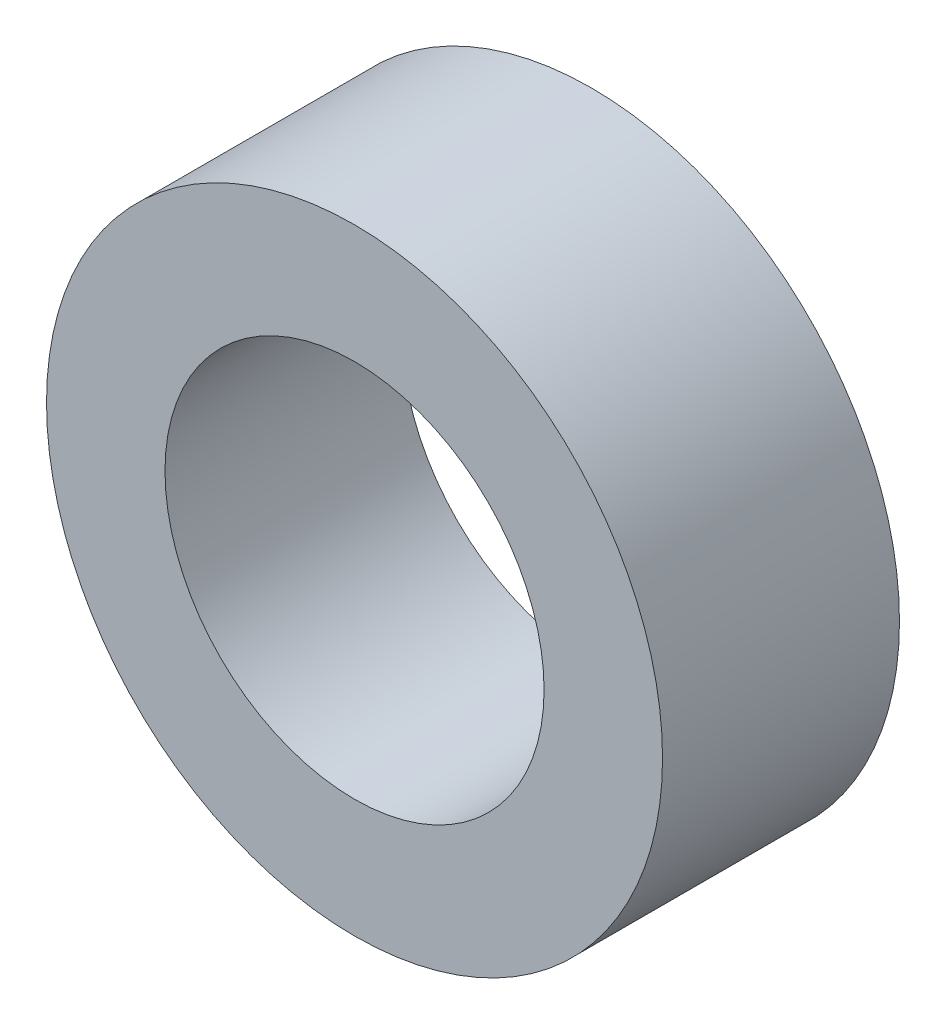
SolidWorks part; units mm, degrees
material "ABS"
ref_plane "Спереди" through (0, 0, 0) normal (0, 0, 1) x (1, 0, 0)
ref_plane "Сверху" through (0, 0, 0) normal (0, 1, 0) x (1, 0, 0)
ref_plane "Справа" through (0, 0, 0) normal (1, 0, 0) x (0, 0, -1)
sketch "Эскиз1" plane through (0, 0, 0) normal (0, 0, 1) x (1, 0, 0)
  circle A0 centre (0, 0) radius 4
  circle A1 centre (0, 0) radius 6.5
  dimension "D1" = 13
  dimension "D2" = 8
extrude "Бобышка-Вытянуть1" add sketch "Эскиз1" along normal blind 5
